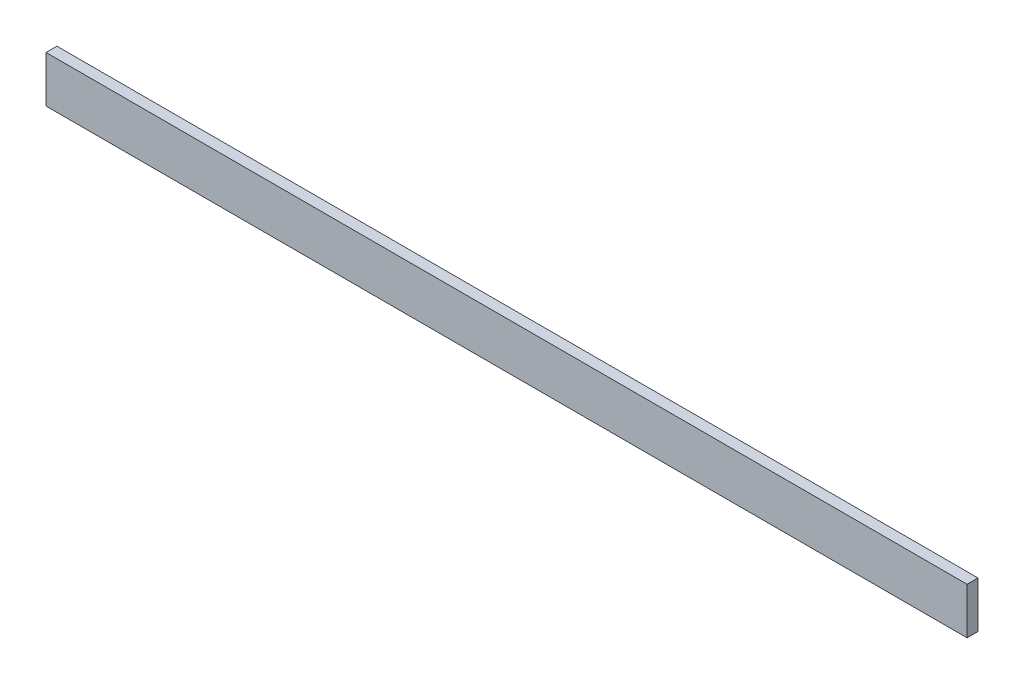
SolidWorks part; units mm, degrees
ref_plane "Front Plane" through (0, 0, 0) normal (0, 0, 1) x (1, 0, 0)
ref_plane "Top Plane" through (0, 0, 0) normal (0, 1, 0) x (1, 0, 0)
ref_plane "Right Plane" through (0, 0, 0) normal (1, 0, 0) x (0, 0, -1)
sketch "Sketch1" plane through (0, 0, 0) normal (0, 0, 1) x (1, 0, 0)
  line L1 (-504.063, -25.4) -> (504.063, -25.4)
  line L2 (-504.063, -25.4) -> (-504.063, 25.4)
  line L3 (-504.063, 25.4) -> (504.063, 25.4)
  line L4 (504.063, -25.4) -> (504.063, 25.4)
  line L5 (-504.063, -25.4) -> (504.063, 25.4) construction
  line L6 (-504.063, 25.4) -> (504.063, -25.4) construction
  point P0 (0, 0)
  dimension "D1" = 1008.126
  dimension "D2" = 50.8
extrude "Boss-Extrude1" add sketch "Sketch1" along normal blind 11.938
